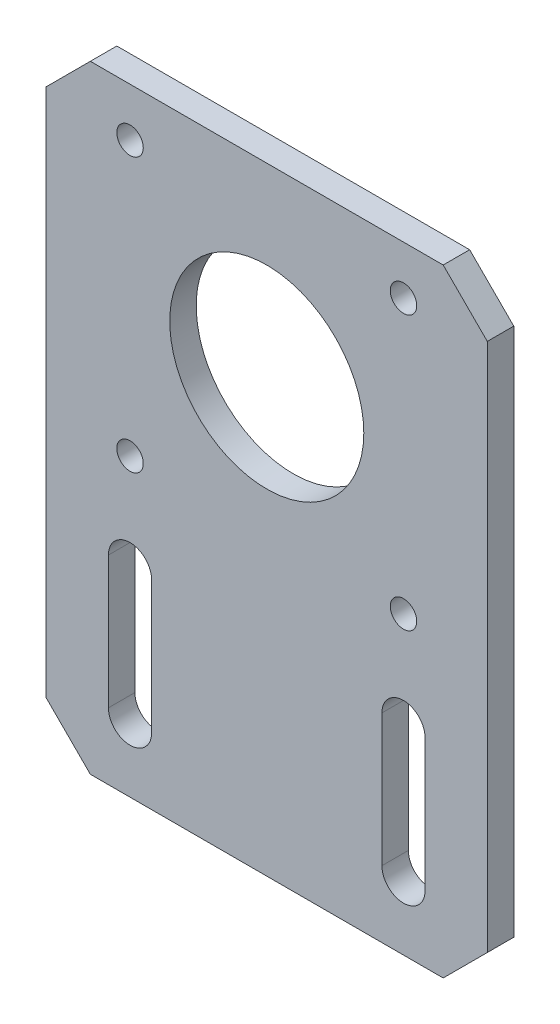
SolidWorks part; units mm, degrees
ref_plane "Front Plane" through (0, 0, 0) normal (0, 0, 1) x (1, 0, 0)
ref_plane "Top Plane" through (0, 0, 0) normal (0, 1, 0) x (1, 0, 0)
ref_plane "Right Plane" through (0, 0, 0) normal (1, 0, 0) x (0, 0, -1)
sketch "Sketch1" plane through (0, 0, 0) normal (0, 0, 1) x (1, 0, 0)
  line L0 (0, 21) -> (0, 0) construction
  line L1 (20, -49) -> (-20, -49)
  line L2 (25, -44) -> (25, 16)
  line L3 (20, 21) -> (-20, 21)
  line L4 (-25, -44) -> (-25, 16)
  line L5 (25, -49) -> (-25, 21) construction
  line L6 (25, 21) -> (-25, -49) construction
  line L7 (0, 0) -> (-25, 0) construction
  line L8 (-15.5, -26.45) -> (-15.5, -41.45) construction
  line L9 (-13.05, -26.45) -> (-13.05, -41.45)
  line L10 (-17.95, -26.45) -> (-17.95, -41.45)
  line L11 (15.5, -26.45) -> (15.5, -41.45) construction
  line L12 (13.05, -26.45) -> (13.05, -41.45)
  line L13 (17.95, -26.45) -> (17.95, -41.45)
  line L14 (25, 16) -> (20, 21)
  line L15 (-20, 21) -> (-25, 16)
  line L16 (25, -44) -> (20, -49)
  line L17 (-20, -49) -> (-25, -44)
  circle A0 centre (0, 0) radius 11
  circle A1 centre (-15.5, 15.5) radius 1.5
  circle A2 centre (15.5, 15.5) radius 1.5
  circle A3 centre (-15.5, -15.5) radius 1.5
  circle A4 centre (15.5, -15.5) radius 1.5
  arc A5 (-13.05, -26.45) -> (-17.95, -26.45) centre (-15.5, -26.45) ccw
  arc A6 (-17.95, -41.45) -> (-13.05, -41.45) centre (-15.5, -41.45) ccw
  arc A7 (13.05, -26.45) -> (17.95, -26.45) centre (15.5, -26.45) cw
  arc A8 (17.95, -41.45) -> (13.05, -41.45) centre (15.5, -41.45) cw
  point P0 (0, -14)
  point P20 (-15.5, -33.95)
  point P25 (-15.5, -17)
  point P26 (-15.5, -24)
  point P29 (15.5, -33.95)
  dimension "D3" = 22
  dimension "D5" = 3
  dimension "D1" = 50
  dimension "D2" = 70
  dimension "D4" = 21
  dimension "D6" = 31
  dimension "D7" = 31
  dimension "D8" = 15
  dimension "D9" = 4.9
  dimension "D10" = 7
extrude "Boss-Extrude1" add sketch "Sketch1" along normal blind 3
